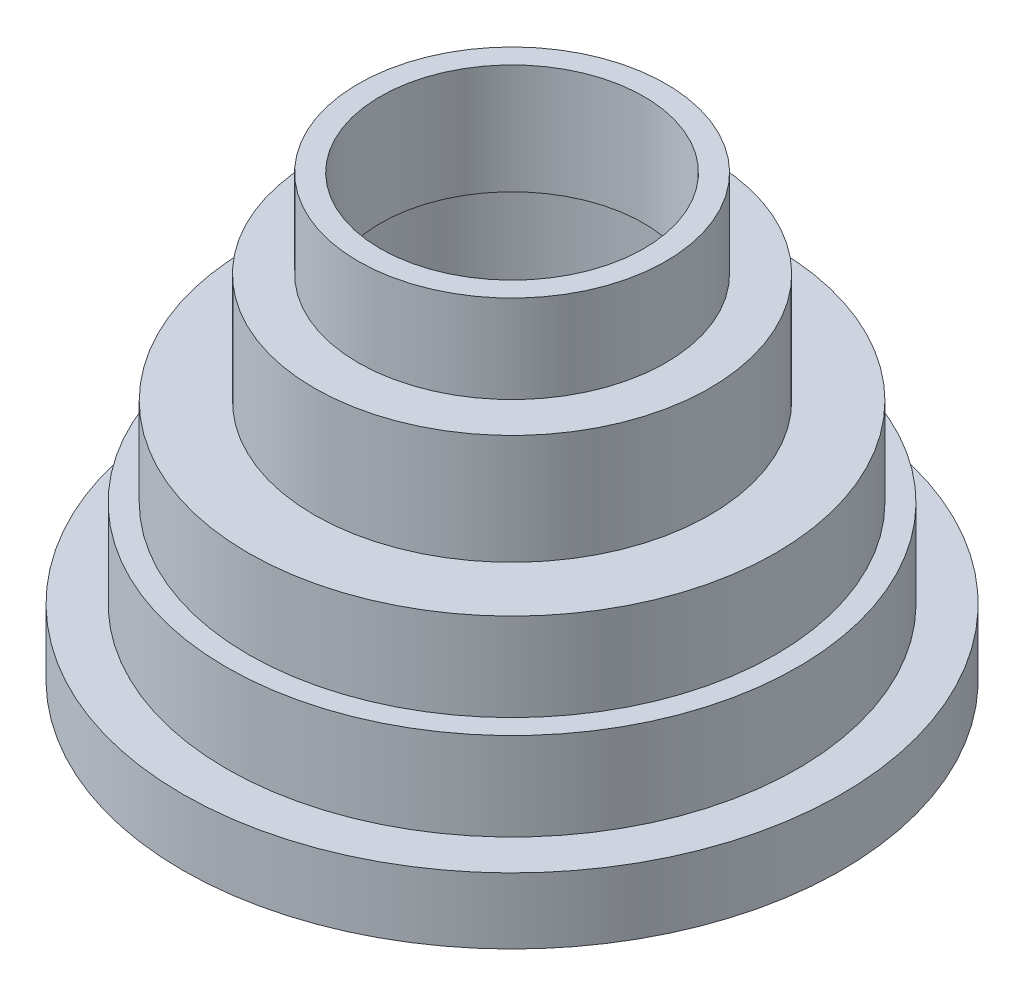
SolidWorks part; units mm, degrees
ref_plane "Front Plane" through (0, 0, 0) normal (0, 0, 1) x (1, 0, 0)
ref_plane "Top Plane" through (0, 0, 0) normal (0, 1, 0) x (1, 0, 0)
ref_plane "Right Plane" through (0, 0, 0) normal (1, 0, 0) x (0, 0, -1)
sketch "Sketch1" plane through (0, 0, 0) normal (0, 0, 1) x (1, 0, 0)
  line L0 (0, 50) -> (0, -50) construction
  line L1 (-75, -52.234) -> (-75, -37.234)
  line L2 (-75, -37.234) -> (-65, -37.234)
  line L3 (-65, -37.234) -> (-65, -17.234)
  line L4 (-65, -17.234) -> (-60, -17.234)
  line L5 (-60, -17.234) -> (-60, 2.766)
  line L6 (-60, 2.766) -> (-45, 2.766)
  line L7 (-45, 2.766) -> (-45, 27.766)
  line L8 (-45, 27.766) -> (-35, 27.766)
  line L9 (-35, 27.766) -> (-35, 47.766)
  point P4 (0, 0)
  dimension "D1" = 100
  dimension "D2" = 15
  dimension "D3" = 20
  dimension "D4" = 20
  dimension "D5" = 25
  dimension "D6" = 20
  dimension "D7" = 75
  dimension "D8" = 10
  dimension "D9" = 5
  dimension "D10" = 15
  dimension "D11" = 10
revolve "Revolve-Thin1" add sketch "Sketch1" angle 360 about L0
